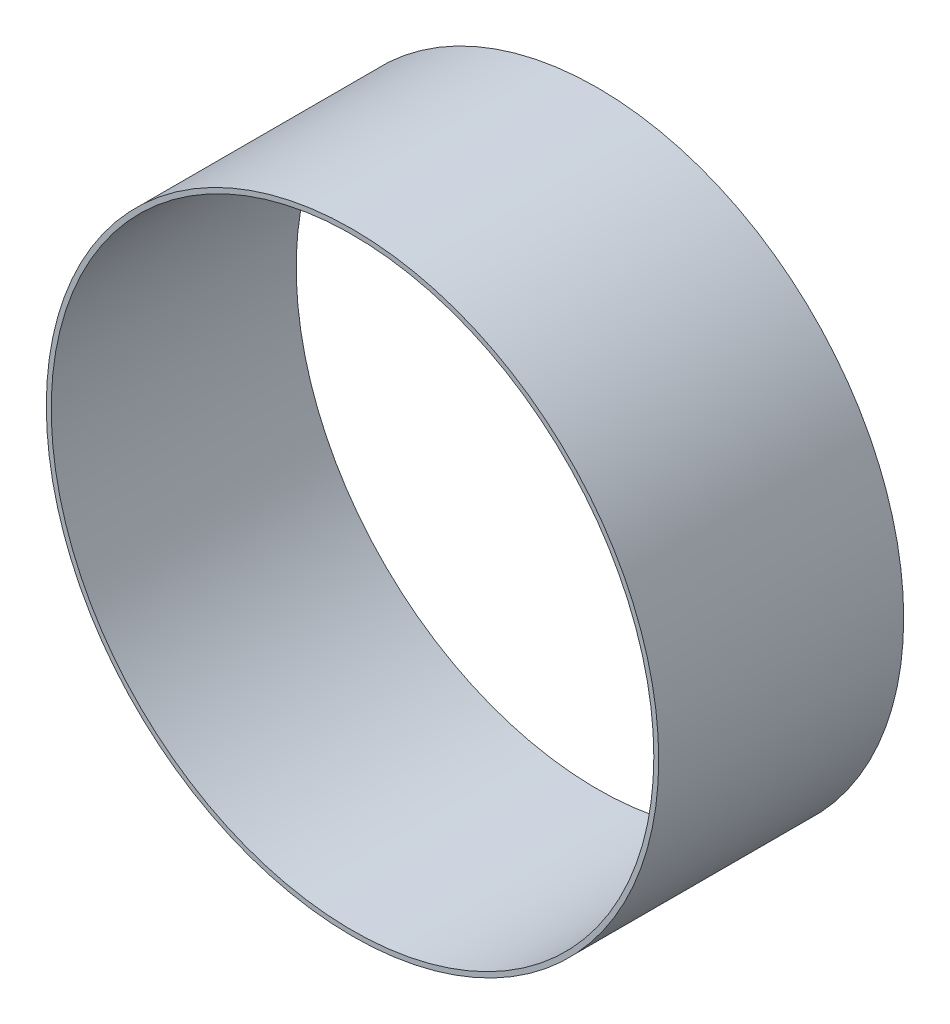
SolidWorks part; units mm, degrees
ref_plane "前视基准面" through (0, 0, 0) normal (0, 0, 1) x (1, 0, 0)
ref_plane "上视基准面" through (0, 0, 0) normal (0, 1, 0) x (1, 0, 0)
ref_plane "右视基准面" through (0, 0, 0) normal (1, 0, 0) x (0, 0, -1)
sketch "草图1" plane through (0, 0, 0) normal (0, 0, 1) x (1, 0, 0)
  circle A0 centre (0, 0) radius 125
  circle A1 centre (0, 0) radius 123
  dimension "D1" = 250
  dimension "D2" = 246
extrude "凸台-拉伸1" add sketch "草图1" along normal blind 100
ref_plane "基准面1" through (0, 0, 0) normal (1, 0, 0) x (0, 0, -1)
